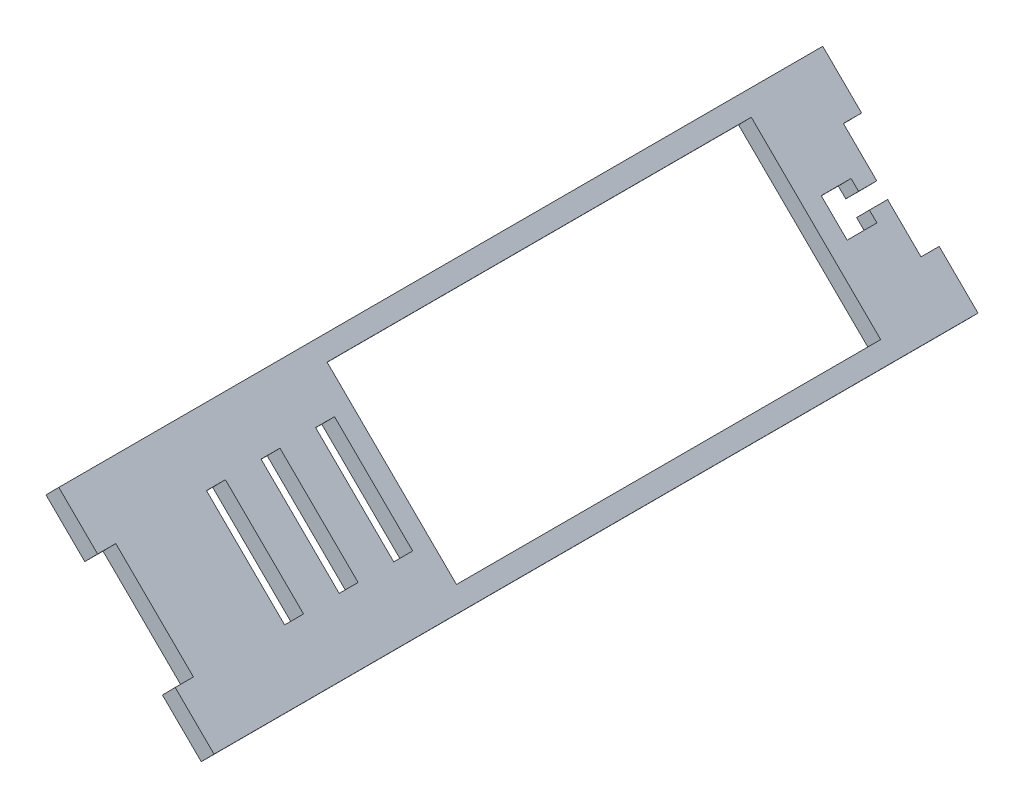
SolidWorks part; units mm, degrees
ref_plane "Front Plane" through (0, 0, 0) normal (0, 0, 1) x (1, 0, 0)
ref_plane "Top Plane" through (0, 0, 0) normal (0, 1, 0) x (1, 0, 0)
ref_plane "Right Plane" through (0, 0, 0) normal (1, 0, 0) x (0, 0, -1)
sketch "Sketch1" plane through (0, 0, 0) normal (0, 0, 1) x (1, 0, 0)
  line L1 (34.8992, 77.9875) -> (77.5734, 35.8102)
  line L2 (34.8992, 77.9875) -> (38.414, 81.5436)
  line L3 (38.414, 81.5436) -> (81.0881, 39.3664)
  line L4 (77.5734, 35.8102) -> (81.0881, 39.3664)
  circle A0 centre (0, 0) radius 80 construction
  point P8 (56.2363, 56.8988)
  dimension "D1" = 160
  dimension "D2" = 5
  dimension "D3" = 60
extrude "Boss-Extrude1" add sketch "Sketch1" along normal blind 200
sketch "Sketch3" plane through (56.2363, 56.8988, 0) normal (-0.703, -0.7112, 0) x (0.7112, -0.703, 0)
  line L0 (-30, 200) -> (30, 200) construction
  line L1 (-30, 200) -> (-15, 200)
  line L2 (-30, 200) -> (-30, 205)
  line L3 (-30, 205) -> (-15, 205)
  line L4 (-15, 200) -> (-15, 205)
  line L5 (-30, 200) -> (-30, 0) construction
  line L6 (0, 200) -> (0, 194.7311) construction
  line L7 (30, 205) -> (15, 205)
  line L8 (15, 200) -> (15, 205)
  line L9 (30, 200) -> (15, 200)
  line L10 (30, 200) -> (30, 205)
  line L11 (-30, 100) -> (-7.68, 100) construction
  line L12 (30, 0) -> (30, -5)
  line L13 (30, 0) -> (15, 0)
  line L14 (15, 0) -> (15, -5)
  line L15 (30, -5) -> (15, -5)
  line L16 (-30, -5) -> (-15, -5)
  line L17 (-15, 0) -> (-15, -5)
  line L18 (-30, 0) -> (-15, 0)
  line L19 (-30, 0) -> (-30, -5)
  dimension "D1" = 5
  dimension "D2" = 15
extrude "Boss-Extrude2" add sketch "Sketch3" against normal blind 5
sketch "Sketch4" plane through (56.2363, 56.8988, 0) normal (-0.703, -0.7112, 0) x (0.7112, -0.703, 0)
  line L5 (-15.1, 175) -> (-15.1, 169.8)
  line L6 (-15.1, 175) -> (15.1, 175)
  line L7 (15.1, 175) -> (15.1, 169.8)
  line L8 (-15.1, 169.8) -> (15.1, 169.8)
  line L9 (-15.1, 160) -> (-15.1, 154.8)
  line L10 (-15.1, 160) -> (15.1, 160)
  line L11 (15.1, 160) -> (15.1, 154.8)
  line L12 (-15.1, 154.8) -> (15.1, 154.8)
  line L13 (-15.1, 145) -> (-15.1, 139.8)
  line L14 (-15.1, 145) -> (15.1, 145)
  line L15 (15.1, 145) -> (15.1, 139.8)
  line L16 (-15.1, 139.8) -> (15.1, 139.8)
  line L17 (-15.1, 130) -> (-15.1, 124.8) construction
  line L18 (-15.1, 130) -> (15.1, 130) construction
  line L19 (15.1, 130) -> (15.1, 124.8) construction
  line L20 (-15.1, 124.8) -> (15.1, 124.8) construction
  line L21 (-15.1, 115) -> (-15.1, 109.8) construction
  line L22 (-15.1, 115) -> (15.1, 115) construction
  line L23 (15.1, 115) -> (15.1, 109.8) construction
  line L24 (-15.1, 109.8) -> (15.1, 109.8) construction
  line L25 (-15.1, 100) -> (-15.1, 94.8) construction
  line L26 (-15.1, 100) -> (15.1, 100) construction
  line L27 (15.1, 100) -> (15.1, 94.8) construction
  line L28 (-15.1, 94.8) -> (15.1, 94.8) construction
  line L29 (-15.1, 85) -> (-15.1, 79.8) construction
  line L30 (-15.1, 85) -> (15.1, 85) construction
  line L31 (15.1, 85) -> (15.1, 79.8) construction
  line L32 (-15.1, 79.8) -> (15.1, 79.8) construction
  line L33 (-15.1, 70) -> (-15.1, 64.8) construction
  line L34 (-15.1, 70) -> (15.1, 70) construction
  line L35 (15.1, 70) -> (15.1, 64.8) construction
  line L36 (-15.1, 64.8) -> (15.1, 64.8) construction
  line L37 (-15.1, 55) -> (-15.1, 49.8) construction
  line L38 (-15.1, 55) -> (15.1, 55) construction
  line L39 (15.1, 55) -> (15.1, 49.8) construction
  line L40 (-15.1, 49.8) -> (15.1, 49.8) construction
  line L41 (-30, 205) -> (-30, -5) construction
  dimension "D1" = 14.9
  dimension "D2" = 45.1
  dimension "D3" = 30
  dimension "D4" = 35.2
  dimension "D5" = 45
  dimension "D6" = 60
  dimension "D7" = 75
  dimension "D8" = 90
  dimension "D9" = 105
  dimension "D10" = 120
  dimension "D11" = 135
  dimension "D12" = 150
extrude "Cut-Extrude1" cut sketch "Sketch4" against normal blind 5
sketch "Sketch5" plane through (59.7511, 60.455, 0) normal (0.703, 0.7112, 0) x (0.7112, -0.703, 0)
  line L0 (15, -200) -> (-15, -200) construction
  line L1 (-2.1, -200) -> (2.1, -200)
  line L2 (-2.1, -200) -> (-2.1, -195)
  line L3 (-2.1, -195) -> (2.1, -195)
  line L4 (2.1, -200) -> (2.1, -195)
  line L5 (15, 0) -> (-15, 0) construction
  line L6 (-5, -195) -> (5, -195)
  line L7 (-5, -195) -> (-5, -186.8)
  line L8 (-5, -186.8) -> (5, -186.8)
  line L9 (5, -195) -> (5, -186.8)
  line L10 (-2.1, 0) -> (2.1, 0)
  line L11 (-2.1, 0) -> (-2.1, -5)
  line L12 (-2.1, -5) -> (2.1, -5)
  line L13 (2.1, 0) -> (2.1, -5)
  line L15 (5, -13.2) -> (-5, -13.2)
  line L16 (5, -13.2) -> (5, -5)
  line L17 (5, -5) -> (-5, -5)
  line L18 (-5, -13.2) -> (-5, -5)
  point P10 (0, -195)
  point P11 (0, -200)
  point P12 (0, -200)
  point P23 (0, -5)
  point P25 (0, -13.2)
  point P26 (0, 0)
  line M56 (15, 0) -> (-15, 0)
  dimension "D1" = 10
  dimension "D2" = 8.2
  dimension "D3" = 4.2
  dimension "D4" = 5
  dimension "D5" = 10
  dimension "D6" = 8.2
  dimension "D7" = 5
  dimension "D8" = 5
  dimension "D10" = 4.2
extrude "Cut-Extrude2" cut sketch "Sketch5" against normal blind 10 contours L18 L15 L16 L17 L12 | L13 L11 L12 M56
sketch "Sketch6" plane through (59.7511, 60.455, 0) normal (0.703, 0.7112, 0) x (0.7112, -0.703, 0)
  line L0 (-30, -205) -> (-30, 5) construction
  line L1 (25, -134.8) -> (-25, -134.8)
  line L2 (25, -134.8) -> (25, -18.2)
  line L3 (25, -18.2) -> (-25, -18.2)
  line L4 (-25, -134.8) -> (-25, -18.2)
  line L5 (-15.1, -139.8) -> (15.1, -139.8) construction
  line L6 (30, -205) -> (30, 5) construction
  line L8 (5, -13.2) -> (-5, -13.2) construction
  dimension "D1" = 5
  dimension "D2" = 5
  dimension "D3" = 5
  dimension "D4" = 5
extrude "Cut-Extrude3" cut sketch "Sketch6" against normal blind 10
